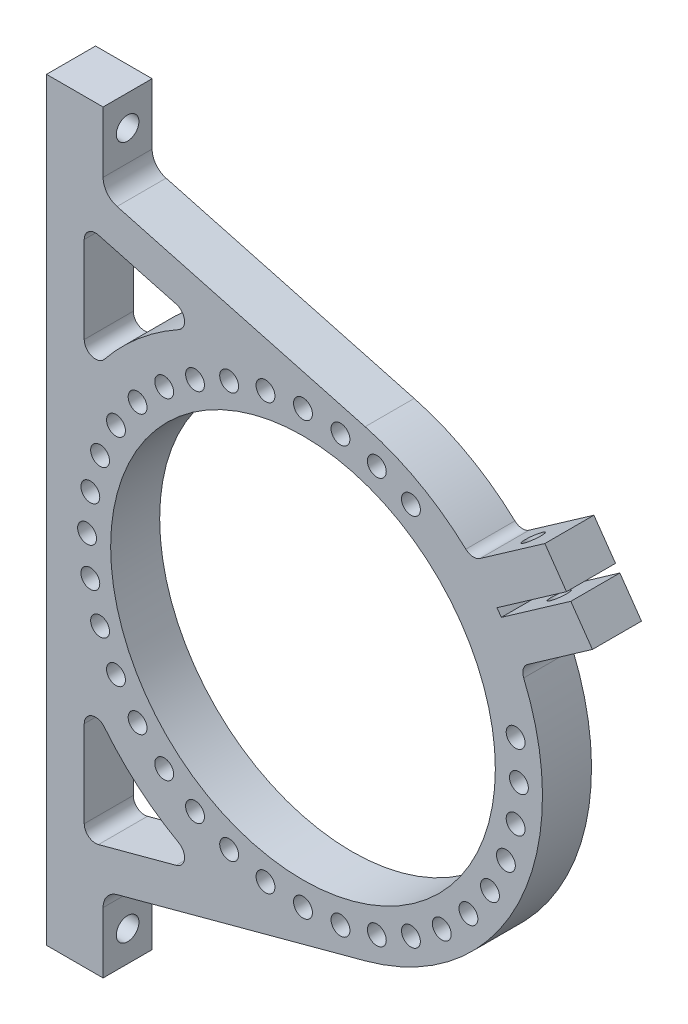
SolidWorks part; units mm, degrees
ref_plane "Front Plane" through (0, 0, 0) normal (0, 0, 1) x (1, 0, 0)
ref_plane "Top Plane" through (0, 0, 0) normal (0, 1, 0) x (1, 0, 0)
ref_plane "Right Plane" through (0, 0, 0) normal (1, 0, 0) x (0, 0, -1)
sketch "Sketch1" plane through (0, 0, 0) normal (0, 0, 1) x (1, 0, 0)
  line L0 (0, 0) -> (0, 200)
  line L1 (0, 200) -> (15, 200)
  line L2 (0, 0) -> (15, 0)
  line L3 (15, 200) -> (15, 180)
  line L4 (15, 0) -> (15, 20)
  line L6 (15, 180) -> (84.4833, 161.3233)
  line L7 (15, 20) -> (84.4833, 38.6767)
  circle A0 centre (68, 100) radius 51
  arc A1 (84.4833, 38.6767) -> (84.4833, 161.3233) centre (68, 100) ccw
  dimension "D7" = 102
  dimension "D8" = 127
  dimension "D1" = 200
  dimension "D2" = 15
  dimension "D3" = 15
  dimension "D4" = 20
  dimension "D5" = 20
extrude "Boss-Extrude1" add sketch "Sketch1" along normal blind 13
fillet "Fillet1" radius 5 2 edges at (15, 20, 6.5) (15, 180, 6.5)
sketch "Sketch2" plane through (0, 0, 13) normal (0, 0, 1) x (1, 0, 0)
  line L0 (68, 100) -> (131.5, 100)
  line L2 (64.8284, 99) -> (141.9038, 152.9688) construction
  line L3 (120.5833, 135.5984) -> (139.0126, 148.5028)
  line L4 (119.4361, 137.2367) -> (137.8655, 150.1411)
  line L5 (119.4361, 137.2367) -> (137.8655, 150.1411)
  line L6 (64.8284, 99) -> (131.5, 99) construction
  line L7 (71.1716, 101) -> (131.5, 101) construction
  line L9 (137.8655, 150.1411) -> (132.1297, 158.3326)
  line L10 (132.1297, 158.3326) -> (112.9204, 144.8821)
  line L11 (71.1716, 101) -> (143.0509, 151.3304) construction
  line L12 (120.5833, 135.5984) -> (139.0126, 148.5028)
  line L13 (139.0126, 148.5028) -> (144.7484, 140.3113)
  line L14 (144.7484, 140.3113) -> (125.5391, 126.8608)
  line L15 (68, 100) -> (142.4773, 152.1496) construction
  arc A0 (84.4833, 38.6767) -> (84.4833, 161.3233) centre (68, 100) ccw construction
  arc M13 (84.4833, 38.6767) -> (84.4833, 161.3233) centre (68, 100) ccw
  dimension "D5" = 10
  dimension "D7" = 10
  dimension "D2" = 1
  dimension "D3" = 1
extrude "Boss-Extrude2" add sketch "Sketch2" against normal blind 13 contours L9 L10 L4 M13 | L14 L13 L3 M13
sketch "Sketch3" plane through (0, 0, 13) normal (0, 0, 1) x (1, 0, 0)
  line L0 (68, 100) -> (119, 100)
  line L1 (93.5, 144.1673) -> (99.75, 154.9926)
  line L2 (118.2252, 108.8561) -> (130.5353, 111.0267)
  circle A0 centre (68, 100) radius 51 construction
  circle A3 centre (96.625, 149.58) radius 2.5
  circle A6 centre (124.3802, 109.9414) radius 2.5
  circle A7 centre (87.5807, 153.7974) radius 2.5
  circle A8 centre (77.9414, 156.3802) radius 2.5
  circle A9 centre (68, 157.25) radius 2.5
  circle A10 centre (58.0586, 156.3802) radius 2.5
  circle A11 centre (48.4193, 153.7974) radius 2.5
  circle A12 centre (39.375, 149.58) radius 2.5
  circle A13 centre (31.2004, 143.856) radius 2.5
  circle A14 centre (24.144, 136.7996) radius 2.5
  circle A15 centre (18.42, 128.625) radius 2.5
  circle A16 centre (14.2026, 119.5807) radius 2.5
  circle A17 centre (11.6198, 109.9414) radius 2.5
  circle A18 centre (10.75, 100) radius 2.5
  circle A19 centre (11.6198, 90.0586) radius 2.5
  circle A20 centre (14.2026, 80.4193) radius 2.5
  circle A21 centre (18.42, 71.375) radius 2.5
  circle A22 centre (24.144, 63.2004) radius 2.5
  circle A23 centre (31.2004, 56.144) radius 2.5
  circle A24 centre (39.375, 50.42) radius 2.5
  circle A25 centre (48.4193, 46.2026) radius 2.5
  circle A26 centre (58.0586, 43.6198) radius 2.5
  circle A27 centre (68, 42.75) radius 2.5
  circle A28 centre (77.9414, 43.6198) radius 2.5
  circle A29 centre (87.5807, 46.2026) radius 2.5
  circle A30 centre (96.625, 50.42) radius 2.5
  circle A31 centre (104.7996, 56.144) radius 2.5
  circle A32 centre (111.856, 63.2004) radius 2.5
  circle A33 centre (117.58, 71.375) radius 2.5
  circle A34 centre (121.7974, 80.4193) radius 2.5
  circle A35 centre (124.3802, 90.0586) radius 2.5
  circle A36 centre (125.25, 100) radius 2.5
  circle A37 centre (124.3802, 109.9414) radius 2.5
  dimension "D2" = 5
  dimension "D3" = 5
  dimension "D1" = 10
  dimension "D4" = 32
extrude "Cut-Extrude1" cut sketch "Sketch3" against normal blind 13 contours A11 | A12 | A3 | A7 | A8 | A9 | A10 | A13 | A14 | A15 | A16 | A17 | A18 | A19 | A20 | A21 | A22 | A23 | A6 | A36 | A35 | A34 | A33 | A32 | A31 | A30 | A29 | A28 | A27 | A26 | A25 | A24
sketch "Sketch4" plane through (15, 0, 0) normal (1, 0, 0) x (0, 0, -1)
  line L0 (0, 183.8335) -> (0, 200) construction
  line L3 (0, 0) -> (0, 16.1665) construction
  circle A0 centre (-6.5, 191.9168) radius 3
  circle A1 centre (-6.5, 8.0832) radius 3
  dimension "D1" = 6
  dimension "D3" = 6.5
  dimension "D4" = 6
  dimension "D2" = 6.5
extrude "Cut-Extrude2" cut sketch "Sketch4" against normal through all
sketch "Sketch5" plane through (-18.304, 26.1408, 0) normal (0.5736, -0.8192, 0) x (0.8192, 0.5736, 0)
  circle A0 centre (187.3251, 6.5) radius 2.5
extrude "Cut-Extrude3" cut sketch "Sketch5" against normal through all
fillet "Fillet2" radius 3 2 edges at (112.9204, 144.8821, 6.5) (125.5391, 126.8608, 6.5)
sketch "Sketch6" plane through (0, 0, 13) normal (0, 0, 1) x (1, 0, 0)
  line L1 (42.1401, 162.35) -> (10, 170.989)
  line L5 (10, 200) -> (10, 0)
  line L6 (10, 170.989) -> (10, 134.529)
  arc A0 (42.1401, 162.35) -> (10, 134.529) centre (68, 100) ccw
  dimension "D1" = 135
  dimension "D3" = 10
extrude "Cut-Extrude4" cut sketch "Sketch6" against normal through all
sketch "Sketch7" plane through (0, 0, 13) normal (0, 0, 1) x (1, 0, 0)
  line L7 (16.1063, 30.6523) -> (10, 29.011)
  line L8 (16.1063, 30.6523) -> (81.8875, 48.3339)
  line L9 (16.1063, 30.6523) -> (42.1401, 37.65)
  line L10 (10, 65.471) -> (10, 29.011)
  arc A0 (10, 65.471) -> (42.1401, 37.65) centre (68, 100) ccw
  dimension "D2" = 10
extrude "Cut-Extrude5" cut sketch "Sketch7" against normal through all
fillet "Fillet3" radius 3 6 edges at (10, 65.471, 6.5) (42.1401, 37.65, 6.5) (10, 29.011, 6.5) (10, 134.529, 6.5) (42.1401, 162.35, 6.5) (10, 170.989, 6.5)
